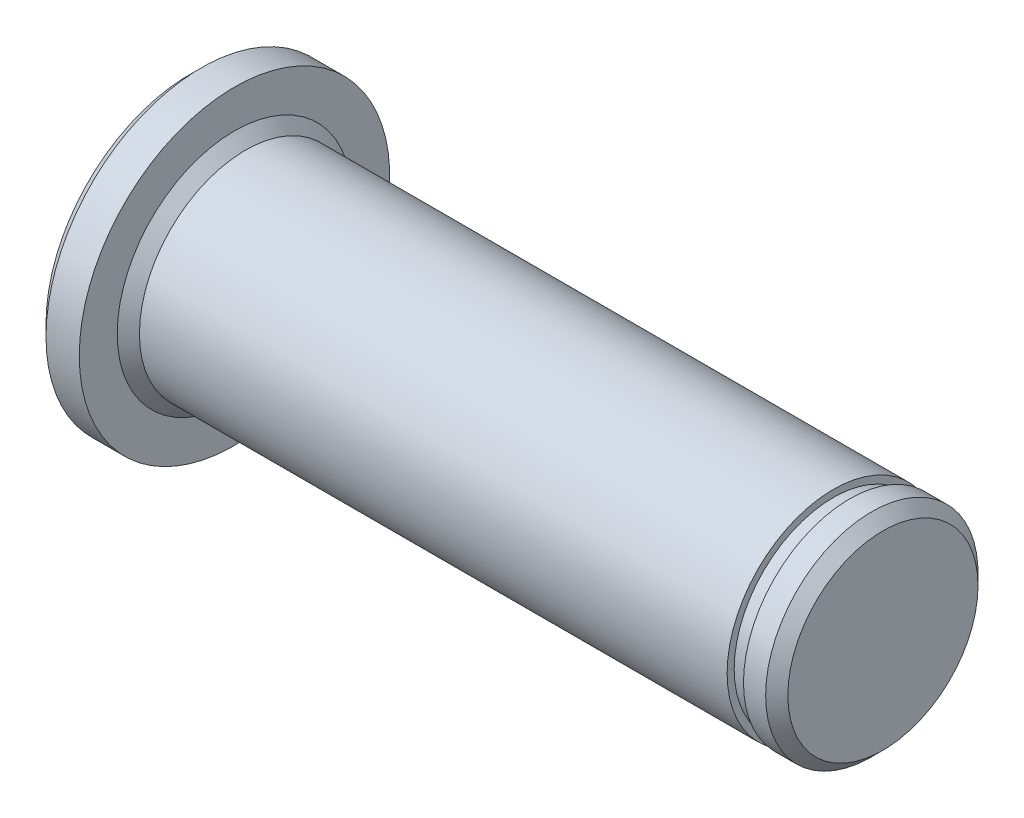
SolidWorks part; units mm, degrees
material "AISI 4340 Steel, normalized"
ref_plane "Front Plane" through (0, 0, 0) normal (0, 0, 1) x (1, 0, 0)
ref_plane "Top Plane" through (0, 0, 0) normal (0, 1, 0) x (1, 0, 0)
ref_plane "Right Plane" through (0, 0, 0) normal (1, 0, 0) x (0, 0, -1)
sketch "Sketch1" plane through (0, 0, 0) normal (0, 0, 1) x (1, 0, 0)
  line L0 (-78.5354, 0) -> (78.5354, 0) construction
  line L1 (0, 4.7875) -> (0, 7)
  line L2 (0, 7) -> (-2, 7)
  line L3 (-2, 7) -> (-2, 0)
  line L4 (0, 4.7875) -> (27, 4.7875)
  line L5 (27, 4.7875) -> (27, 4.47)
  line L6 (27, 4.47) -> (27.737, 4.47)
  line L7 (27.737, 4.47) -> (27.737, 4.7875)
  line L8 (27.737, 4.7875) -> (29.237, 4.7875)
  line L9 (29.237, 4.7875) -> (29.237, 0)
  line L10 (29.237, 0) -> (-2, 0)
  dimension "D1" = 14
  dimension "D2" = 2
  dimension "D3" = 1.5
  dimension "D4" = 9.575
  dimension "D5" = 27
  dimension "D6" = 8.94
  dimension "D7" = 0.737
revolve "Revolve1" add sketch "Sketch1" angle 360 about L0
chamfer "Chamfer1" distance 0.5 angle 45 3 edges at (-2, 0, 7) (0, 0, 4.7875) (29.237, 0, 4.7875)
